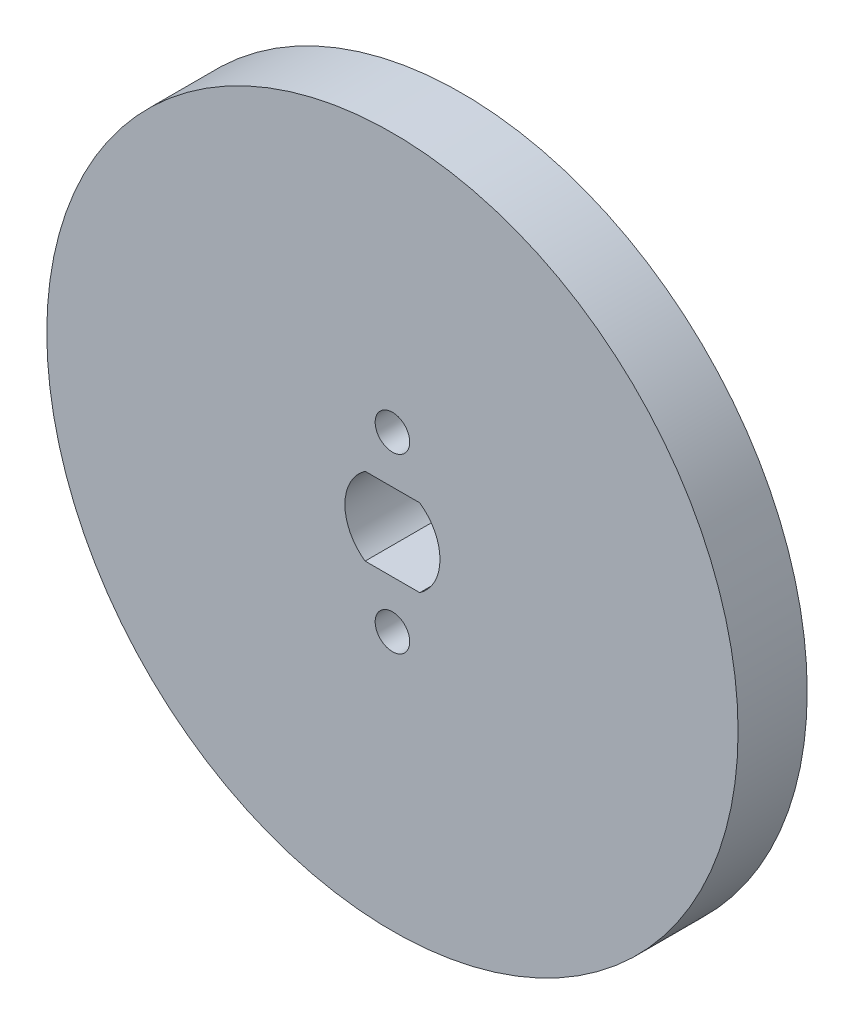
SolidWorks part; units mm, degrees
ref_plane "Спереди" through (0, 0, 0) normal (0, 0, 1) x (1, 0, 0)
ref_plane "Сверху" through (0, 0, 0) normal (0, 1, 0) x (1, 0, 0)
ref_plane "Справа" through (0, 0, 0) normal (1, 0, 0) x (0, 0, -1)
sketch "Эскиз1" plane through (0, 0, 0) normal (0, 0, 1) x (1, 0, 0)
  circle A0 centre (0, 0) radius 20
  dimension "D1" = 40
extrude "Бобышка-Вытянуть1" add sketch "Эскиз1" along normal blind 4 contours A0
sketch "Эскиз2" plane through (0, 0, 4) normal (0, 0, 1) x (1, 0, 0)
  line L0 (-2.75, 0) -> (2.75, 0) construction
  line L3 (-1.5811, 2.25) -> (1.5811, 2.25)
  line L4 (-1.5811, -2.25) -> (1.5811, -2.25)
  arc A2 (-1.5811, 2.25) -> (-1.5811, -2.25) centre (0, 0) ccw
  arc A3 (1.5811, -2.25) -> (1.5811, 2.25) centre (0, 0) ccw
  circle A4 centre (0, 5) radius 1
  circle A5 centre (0, -5) radius 1
  dimension "D2" = 4.5
  dimension "D1" = 5.5
  dimension "D3" = 2
  dimension "D4" = 10
extrude "Вырез-Вытянуть1" cut sketch "Эскиз2" against normal blind 4
